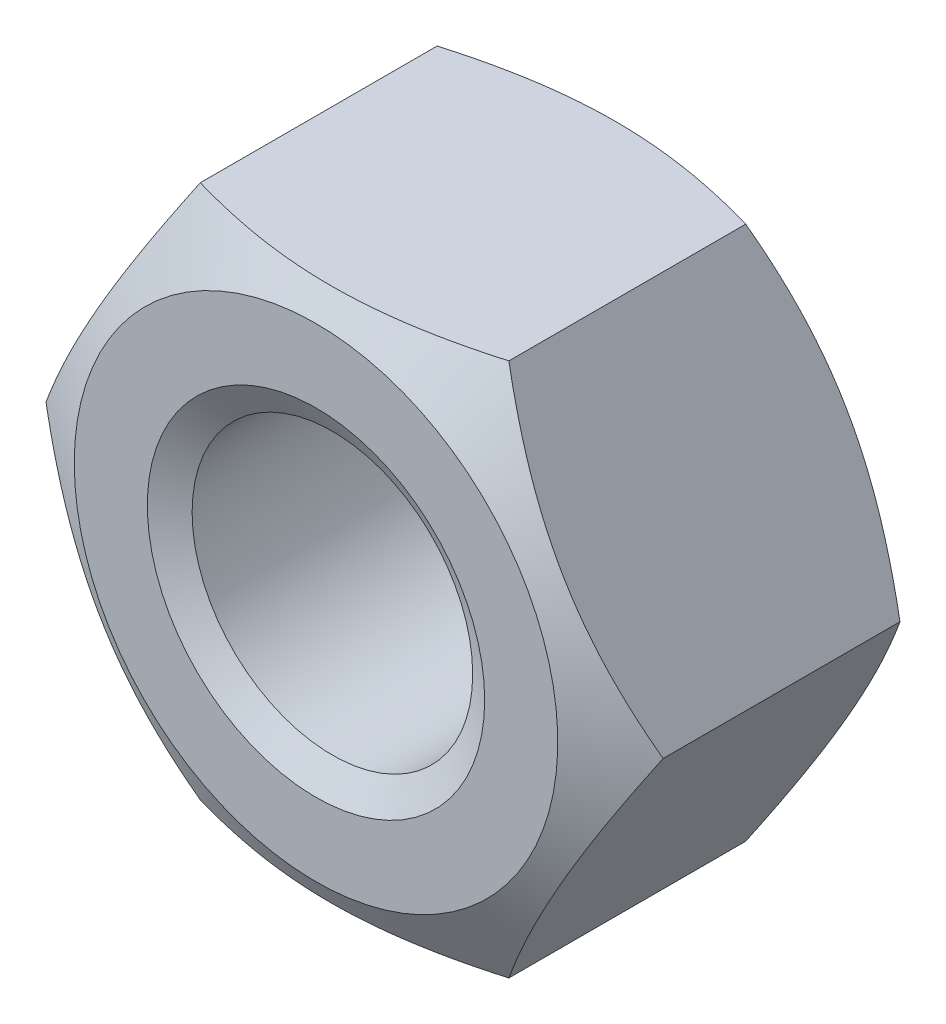
SolidWorks part; units mm, degrees
ref_plane "Front Plane" through (0, 0, 0) normal (0, 0, 1) x (1, 0, 0)
ref_plane "Top Plane" through (0, 0, 0) normal (0, 1, 0) x (1, 0, 0)
ref_plane "Right Plane" through (0, 0, 0) normal (1, 0, 0) x (0, 0, -1)
sketch "草图1" plane through (0, 0, 0) normal (0, 0, 1) x (1, 0, 0)
  line L1 (2.3094, 4) -> (-2.3094, 4)
  line L2 (-2.3094, 4) -> (-4.6188, 0)
  line L3 (-4.6188, 0) -> (-2.3094, -4)
  line L4 (-2.3094, -4) -> (2.3094, -4)
  line L5 (2.3094, -4) -> (4.6188, 0)
  line L6 (4.6188, 0) -> (2.3094, 4)
  circle A0 centre (0, 0) radius 4 construction
  dimension "D1" = 8
extrude "凸台-拉伸1" add sketch "草图1" along normal blind 4.7
hole_wizard "M5 螺纹孔1" positions "草图3" profile "草图2" tap size "M5" standard "GB" end condition through all
sketch "草图3" plane through (0, 0, 4.7) normal (0, 0, 1) x (1, 0, 0)
  point P0 (0, 0)
sketch "草图2" plane through (0, 0, 4.7) normal (1, 0, 0) x (0, -1, 0)
  line L0 (0, 0) -> (0, 4.7)
  line L1 (0, 4.7) -> (2.525, 4.7)
  line L2 (2.1, 4.4546) -> (2.1, 0.2454)
  line L3 (2.1, 0.2454) -> (2.525, 0)
  line L5 (2.525, 0) -> (0, 0)
  line L6 (-2.1, 0.2454) -> (-2.525, 0) construction
  line L7 (2.525, 4.7) -> (2.1, 4.4546)
  line L8 (-2.525, 4.7) -> (-2.1, 4.4546) construction
  line L11 (0, -6.35) -> (0, 107.95) construction
  dimension "通孔螺纹孔钻头直径" = 4.2
  dimension "通孔螺纹孔钻头深度" = 4.7
  dimension "近端锥形沉头孔直径" = 5.05
  dimension "近端锥形沉头孔角度" = 120
  dimension "远端锥形沉头孔直径" = 5.05
  dimension "远端锥形沉头孔角度" = 120
cosmetic thread "孔螺蚊线1" parameters "D2"=5
sketch "草图4" plane through (0, 0, 0) normal (0, 1, 0) x (1, 0, 0)
  line L0 (-4.6188, -0.5774) -> (-3.6188, 0)
  line L1 (-4.6188, -4.7) -> (-4.6188, 0) construction
  line L2 (-2.3094, 0) -> (-4.6188, 0) construction
  line L3 (0, 0) -> (0, -5.4761) construction
  line L4 (-4.6188, -0.5774) -> (-4.6188, 0)
  line L5 (-4.6188, 0) -> (-3.6188, 0)
  line L6 (-4.6188, -2.35) -> (4.6188, -2.35) construction
  line L7 (4.6188, -4.7) -> (4.6188, 0) construction
  line L8 (-4.6188, -4.7) -> (-3.6188, -4.7)
  line L9 (-4.6188, -4.1226) -> (-4.6188, -4.7)
  line L10 (-4.6188, -4.1226) -> (-3.6188, -4.7)
  dimension "D1" = 1
  dimension "D2" = 30
revolve "切除-旋转1" cut sketch "草图4" angle 360 about L3
